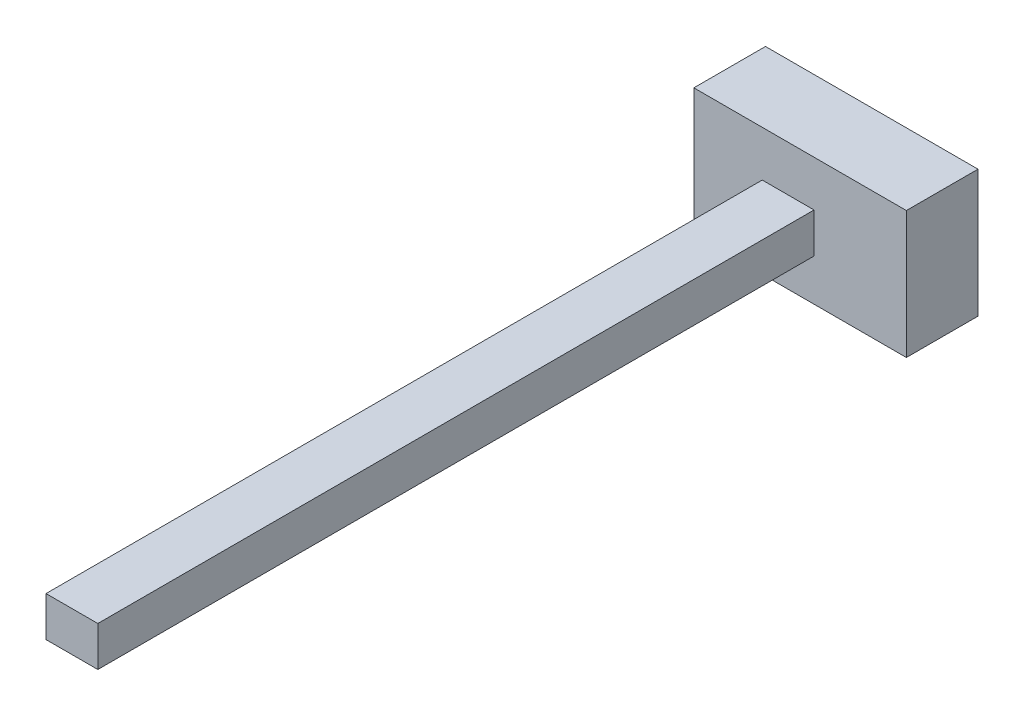
SolidWorks part; units mm, degrees
ref_plane "前基準面" through (0, 0, 0) normal (0, 0, 1) x (1, 0, 0)
ref_plane "上基準面" through (0, 0, 0) normal (0, 1, 0) x (1, 0, 0)
ref_plane "右基準面" through (0, 0, 0) normal (1, 0, 0) x (0, 0, -1)
sketch "草圖1" plane through (0, 0, 0) normal (0, 0, 1) x (1, 0, 0)
  line L1 (0, 0) -> (29.6709, 0)
  line L2 (0, 0) -> (0, 17.7758)
  line L3 (0, 17.7758) -> (29.6709, 17.7758)
  line L4 (29.6709, 0) -> (29.6709, 17.7758)
extrude "填料-伸長1" add sketch "草圖1" along normal blind 10
sketch "草圖2" plane through (0, 0, 10) normal (0, 0, 1) x (1, 0, 0)
  line L1 (9.5469, 11.3991) -> (16.7831, 11.3991)
  line L2 (9.5469, 11.3991) -> (9.5469, 5.8311)
  line L3 (9.5469, 5.8311) -> (16.7831, 5.8311)
  line L4 (16.7831, 11.3991) -> (16.7831, 5.8311)
extrude "填料-伸長3" add sketch "草圖2" along normal blind 100
